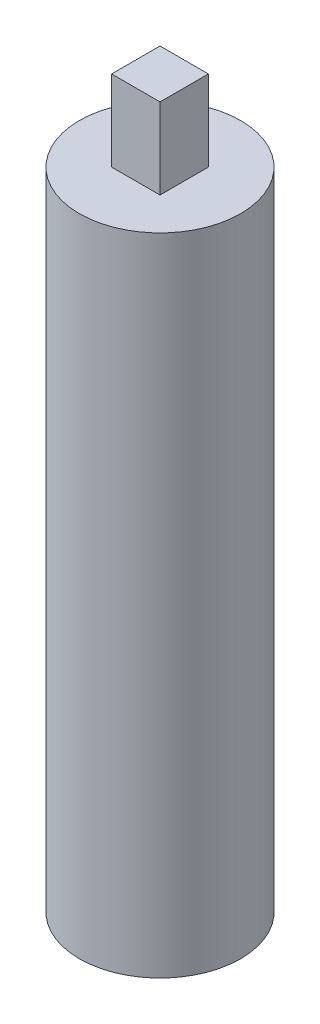
SolidWorks part; units mm, degrees
ref_plane "Front Plane" through (0, 0, 0) normal (0, 0, 1) x (1, 0, 0)
ref_plane "Top Plane" through (0, 0, 0) normal (0, 1, 0) x (1, 0, 0)
ref_plane "Right Plane" through (0, 0, 0) normal (1, 0, 0) x (0, 0, -1)
sketch "Sketch1" plane through (0, 0, 0) normal (0, 1, 0) x (1, 0, 0)
  circle A0 centre (0, 0) radius 5
extrude "Boss-Extrude1" add sketch "Sketch1" along normal blind 40
sketch "Sketch2" plane through (0, 40, 0) normal (0, 1, 0) x (1, 0, 0)
  line L1 (-1.5, 1.5) -> (1.5, 1.5)
  line L2 (-1.5, 1.5) -> (-1.5, -1.5)
  line L3 (-1.5, -1.5) -> (1.5, -1.5)
  line L4 (1.5, 1.5) -> (1.5, -1.5)
  dimension "D1" = 3
  dimension "D2" = 3
  dimension "D3" = 1.5
  dimension "D4" = 1.5
extrude "Boss-Extrude2" add sketch "Sketch2" along normal blind 5
